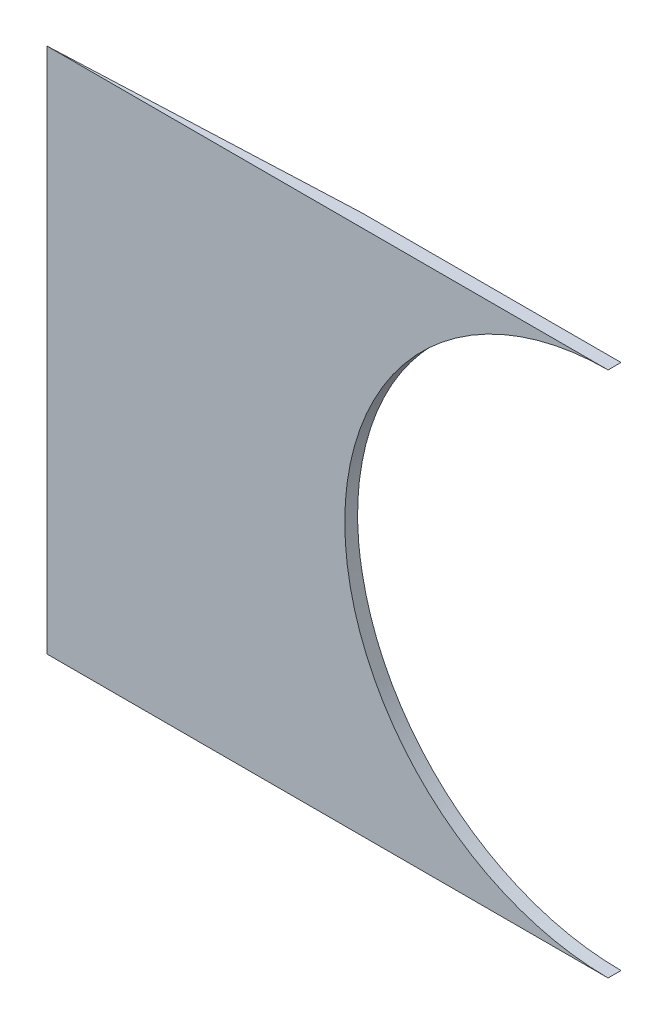
SolidWorks part; units mm, degrees
ref_plane "Front Plane" through (0, 0, 0) normal (0, 0, 1) x (1, 0, 0)
ref_plane "Top Plane" through (0, 0, 0) normal (0, 1, 0) x (1, 0, 0)
ref_plane "Right Plane" through (0, 0, 0) normal (1, 0, 0) x (0, 0, -1)
sketch "Sketch1" plane through (0, 0, 0) normal (0, 0, 1) x (1, 0, 0)
  line L0 (0, 61) -> (-130, 61)
  line L1 (-130, 61) -> (-130, -61)
  line L2 (-130, -61) -> (0, -61)
  arc A0 (0, 61) -> (0, -61) centre (0, 0) ccw
  dimension "D1" = 122
  dimension "D2" = 130
extrude "Boss-Extrude1" add sketch "Sketch1" along normal blind 3 contours A0 L2 L1 L0
ref_plane "Plane3" through (0, -61, 0) normal (0, -1, 0) x (-1, 0, 0)
sketch "Sketch3" plane through (0, -61, 0) normal (0, -1, 0) x (-1, 0, 0)
  line L0 (130, -3) -> (60, 0)
  line L1 (60, 0) -> (130, 0)
  line L2 (130, 0) -> (130, -3)
  line L4 (130, 0) -> (0, 0) construction
  dimension "D1" = 60
extrude "Cut-Extrude1" cut sketch "Sketch3" against normal blind 123
